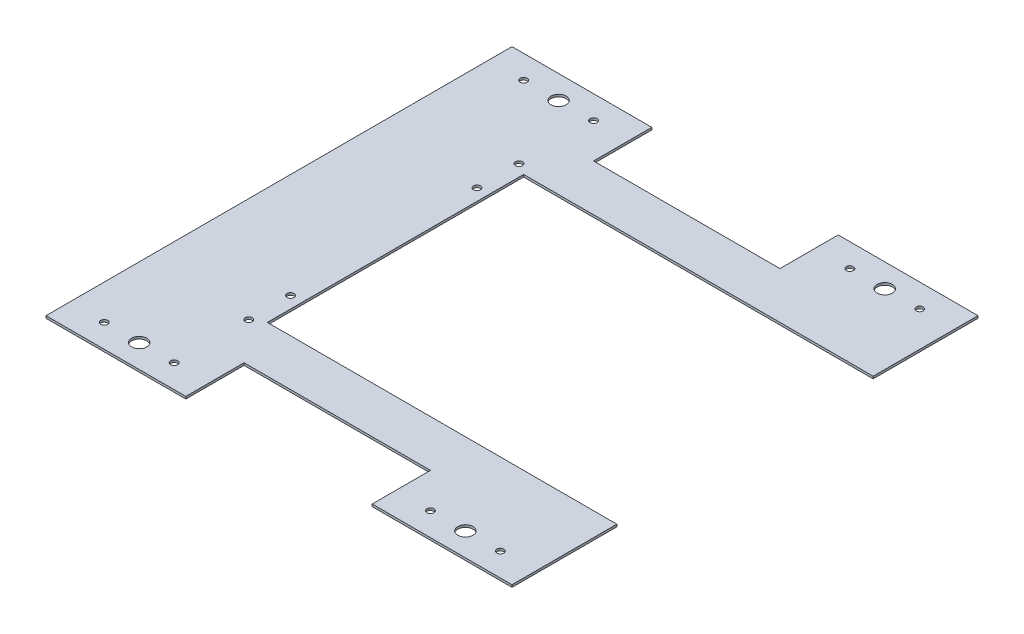
SolidWorks part; units mm, degrees
ref_plane "Plan de face" through (0, 0, 0) normal (0, 0, 1) x (1, 0, 0)
ref_plane "Plan de dessus" through (0, 0, 0) normal (0, 1, 0) x (1, 0, 0)
ref_plane "Plan de droite" through (0, 0, 0) normal (1, 0, 0) x (0, 0, -1)
sketch "Esquisse1" plane through (0, 0, 0) normal (0, 1, 0) x (1, 0, 0)
  line L0 (-40, 100) -> (-40, 75)
  line L1 (40, -100) -> (100, -100)
  line L2 (-100, -100) -> (-100, 100)
  line L3 (40, 100) -> (100, 100)
  line L4 (100, -100) -> (100, -55)
  line L5 (-100, 100) -> (-40, 100)
  line L6 (40, -100) -> (40, -75)
  line L7 (-40, 75) -> (40, 75)
  line L8 (40, 100) -> (40, 75)
  line L9 (-40, -75) -> (40, -75)
  line L10 (-40, -100) -> (-40, -75)
  line L11 (-100, -100) -> (-40, -100)
  line L12 (100, 55) -> (-50, 55)
  line L13 (-50, 55) -> (-50, -55)
  line L14 (100, 0) -> (-100, 0) construction
  line L15 (100, -55) -> (-50, -55)
  line L16 (0, 75) -> (0, 0) construction
  line L17 (100, 100) -> (100, 55)
  circle A0 centre (-85, 90) radius 1.5
  circle A1 centre (-55, 90) radius 1.5
  circle A2 centre (-55, -90) radius 1.5
  circle A3 centre (-85, -90) radius 1.5
  circle A4 centre (55, -90) radius 1.5
  circle A5 centre (85, -90) radius 1.5
  circle A6 centre (-55, -58) radius 1.5
  circle A7 centre (-55, -40) radius 1.5
  circle A8 centre (-55, 40) radius 1.5
  circle A9 centre (-55, 58) radius 1.5
  circle A10 centre (-70, -90) radius 3.25
  circle A11 centre (70, -90) radius 3.25
  circle A12 centre (70, 90) radius 3.25
  circle A13 centre (-70, 90) radius 3.25
  circle A34 centre (55, 90) radius 1.5
  circle A35 centre (85, 90) radius 1.5
  point P10 (0, 75)
  point P35 (-50, 0)
  dimension "D11" = 55
  dimension "D12" = 50
  dimension "D13" = 100
  dimension "D14" = 3
  dimension "D15" = 3
  dimension "D16" = 3
  dimension "D17" = 3
  dimension "D18" = 6.5
  dimension "D20" = 6.5
  dimension "D19" = 6.5
  dimension "D4" = 30
  dimension "D5" = 90
  dimension "D3" = 3
  dimension "D7" = 3
  dimension "D8" = 90
  dimension "D21" = 6.5
  dimension "D1" = 55
  dimension "D2" = 100
  dimension "D6" = 40
  dimension "D9" = 100
  dimension "D10" = 25
extrude "Boss.-Extru.1" add sketch "Esquisse1" along normal blind 1
